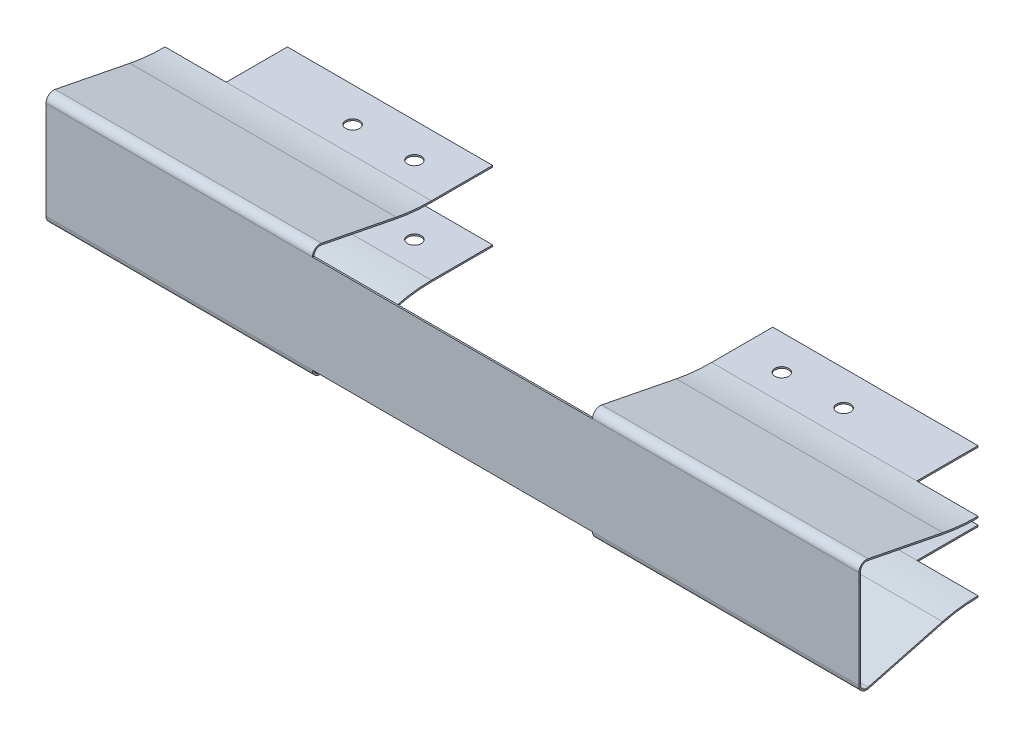
SolidWorks part; units mm, degrees
ref_plane "Front Plane" through (0, 0, 0) normal (0, 0, 1) x (1, 0, 0)
ref_plane "Top Plane" through (0, 0, 0) normal (0, 1, 0) x (1, 0, 0)
ref_plane "Right Plane" through (0, 0, 0) normal (1, 0, 0) x (0, 0, -1)
sketch "Sketch1" plane through (0, 0, 0) normal (1, 0, 0) x (0, 0, -1)
  line L0 (-14.22, 5) -> (-22.22, 5) construction
  line L1 (-24.22, 8) -> (-22.22, 8) construction
  line L2 (-24.22, 8) -> (-24.22, -8) construction
  line L3 (-24.22, -8) -> (-22.22, -8) construction
  line L4 (-14.22, 5) -> (-14.22, 3) construction
  line L5 (-24.22, 8) -> (-14.22, -5) construction
  line L6 (-24.22, -8) -> (-14.22, 5) construction
  line L7 (-22.22, 5) -> (-22.22, 8) construction
  line L8 (-14.22, 3) -> (-21.22, 3) construction
  line L9 (-21.22, 3) -> (-21.22, -3) construction
  line L10 (-21.22, -3) -> (-14.22, -3) construction
  line L11 (-14.22, -5) -> (-22.22, -5) construction
  line L12 (-22.22, -5) -> (-22.22, -8) construction
  line L13 (-14.22, -3) -> (-14.22, -5) construction
  line L14 (-24.22, 8) -> (-24.22, -8)
  line L15 (-10.8136, 6.5687) -> (-23.0262, 8.981)
  line L16 (-5, 5) -> (-5, -5) construction
  line L17 (-5, -5) -> (5, -5) construction
  line L18 (5, 5) -> (5, -5) construction
  line L19 (-5, 5) -> (5, -5) construction
  line L20 (-5, -5) -> (5, 5) construction
  line L21 (-5, 5) -> (5, 5) construction
  line L22 (-5, 5) -> (-5, 6) construction
  line L23 (-5, 6) -> (5, 6) construction
  line L24 (5, 5) -> (5, 6) construction
  line L25 (-10.8136, -5.7553) -> (-22.9645, -8.9668)
  line L26 (-5, -5) -> (5, -5)
  line L27 (-5, 6.25) -> (5, 6.25)
  line L28 (-5, 6) -> (5, 6)
  line L29 (-10.7651, 6.8139) -> (-22.9778, 9.2263)
  line L30 (-24.47, 8) -> (-24.47, -8)
  line L31 (-10.7497, -5.997) -> (-22.9006, -9.2085)
  line L32 (-5, -5.25) -> (5, -5.25)
  line L33 (5, 6.25) -> (5, 6)
  line L34 (5, -5) -> (5, -5.25)
  arc A0 (-24.22, -8) -> (-22.9645, -8.9668) centre (-23.22, -8) ccw
  arc A1 (-23.0262, 8.981) -> (-24.22, 8) centre (-23.22, 8) ccw
  arc A2 (-5, 6.25) -> (-10.7651, 6.8139) centre (-5, 36) cw
  arc A3 (-22.9778, 9.2263) -> (-24.47, 8) centre (-23.22, 8) ccw
  arc A4 (-24.47, -8) -> (-22.9006, -9.2085) centre (-23.22, -8) ccw
  arc A5 (-5, -5.25) -> (-10.7497, -5.997) centre (-5, -27.7512) ccw
  arc A6 (-5, -5) -> (-10.8136, -5.7553) centre (-5, -27.7512) ccw
  arc A7 (-5, 6) -> (-10.8136, 6.5687) centre (-5, 36) cw
  point P0 (-18.0662, 0)
  point P1 (0, 0)
  dimension "D13" = 30
  dimension "D17" = 1
  dimension "D1" = 16
  dimension "D2" = 10
  dimension "D3" = 2
  dimension "D4" = 2
  dimension "D5" = 2
  dimension "D6" = 3
  dimension "D7" = 6
  dimension "D8" = 3
  dimension "D9" = 10
  dimension "D10" = 10
  dimension "D11" = 16.22
  dimension "D12" = 1
  dimension "D14" = 0.25
extrude "Extrude1" add sketch "Sketch1" along normal mid plane 132.92
sketch "Sketch2" plane through (0, 0, 0) normal (0, 0, 1) x (1, 0, 0)
  line L0 (-22.9, 8) -> (-22.9, 9.25)
  line L1 (-22.9, 8) -> (22.9, 8)
  line L2 (-22.9, 8) -> (-22.9, -8) construction
  line L3 (-22.9, -8) -> (22.9, -8)
  line L4 (22.9, 8) -> (22.9, -8) construction
  line L5 (-22.9, 8) -> (22.9, -8) construction
  line L6 (-22.9, -8) -> (22.9, 8) construction
  line L7 (66.46, 9.25) -> (-66.46, 9.25) construction
  line L8 (-22.9, 9.25) -> (22.9, 9.25)
  line L9 (22.9, 9.25) -> (22.9, 8)
  line L10 (22.9, -8) -> (22.9, -9.25)
  line L11 (-66.46, -9.25) -> (66.46, -9.25) construction
  line L12 (22.9, -9.25) -> (-22.9, -9.25)
  line L13 (-22.9, -9.25) -> (-22.9, -8)
  point P0 (0, 0)
  dimension "D1" = 45.8
  dimension "D2" = 16
extrude "Cut-Extrude1" cut sketch "Sketch2" along normal through all
sketch "Sketch3" plane through (0, 0, 0) normal (0, 1, 0) x (1, 0, 0)
  line L0 (-22.9, -16.7696) -> (-22.9, -22.9778) construction
  line L1 (-22.9, -24.22) -> (22.9, -24.22)
  line L2 (-22.9, -24.22) -> (-22.9, 5)
  line L3 (-22.9, 5) -> (22.9, 5)
  line L4 (22.9, -24.22) -> (22.9, 5)
  line L5 (-22.9, -24.22) -> (22.9, 5) construction
  line L6 (-22.9, 5) -> (22.9, -24.22) construction
  line L7 (66.46, 5) -> (-66.46, 5) construction
  line L9 (22.9, -24.22) -> (-22.9, -24.22) construction
  point P0 (0, -9.61)
extrude "Cut-Extrude2" cut sketch "Sketch3" against normal through all and the other way through all
sketch "Sketch4" plane through (0, 0, 0) normal (0, 1, 0) x (1, 0, 0)
  line L0 (-66.46, 5) -> (-66.46, -5) construction
  line L1 (-22.9, 5) -> (-66.46, 5) construction
  line L3 (0, 0) -> (0, -20.9406) construction
  line L4 (-22.9, -5) -> (-66.46, -5) construction
  line L5 (-66.46, 5) -> (-56.46, 5)
  line L6 (-66.46, 5) -> (-66.46, -5)
  line L7 (-66.46, -5) -> (-56.46, -5)
  line L8 (-56.46, 5) -> (-56.46, -5)
  line L9 (-66.46, 5) -> (-56.46, -5) construction
  line L10 (-66.46, -5) -> (-56.46, 5) construction
  line L11 (66.46, -5) -> (56.46, 5) construction
  line L12 (66.46, 5) -> (56.46, -5) construction
  line L13 (66.46, 5) -> (56.46, 5)
  line L14 (66.46, 5) -> (66.46, -5)
  line L15 (66.46, -5) -> (56.46, -5)
  line L16 (56.46, 5) -> (56.46, -5)
  circle A0 centre (-61.46, 0) radius 1.75 construction
  circle A1 centre (-40.14, -0.65) radius 1.125
  circle A2 centre (-30.04, -0.65) radius 1.125
  circle A3 centre (30.04, -0.65) radius 1.125
  circle A4 centre (40.14, -0.65) radius 1.125
  dimension "D3" = 3.5
  dimension "D4" = 2.25
  dimension "D5" = 2.25
  dimension "D1" = 5
  dimension "D2" = 5
  dimension "D6" = 10.1
  dimension "D7" = 21.32
  dimension "D8" = 0.65
extrude "Cut-Extrude3" cut sketch "Sketch4" against normal through all and the other way through all
